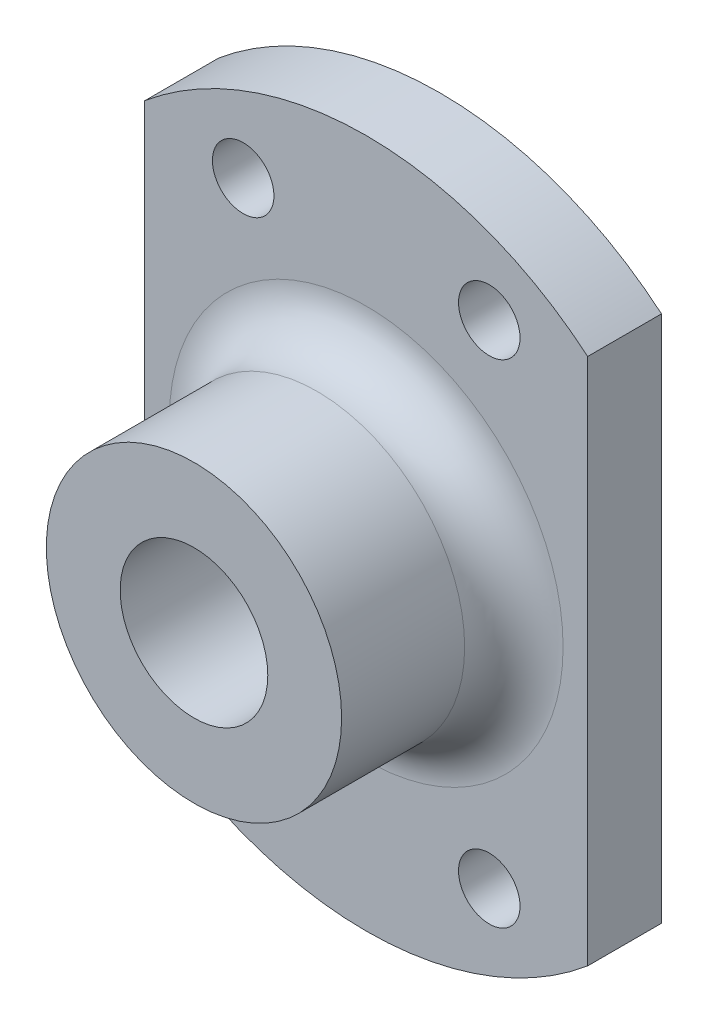
SolidWorks part; units mm, degrees
ref_plane "Front Plane" through (0, 0, 0) normal (0, 0, 1) x (1, 0, 0)
ref_plane "Top Plane" through (0, 0, 0) normal (0, 1, 0) x (1, 0, 0)
ref_plane "Right Plane" through (0, 0, 0) normal (1, 0, 0) x (0, 0, -1)
sketch "Sketch1" plane through (0, 0, 0) normal (0, 0, 1) x (1, 0, 0)
  line L0 (-9, 10.7238) -> (-9, -10.7238)
  line L1 (9, 10.7238) -> (9, -10.7238)
  line L2 (-9, 0) -> (9, 0) construction
  line L3 (-5, 10) -> (5, -10) construction
  line L4 (-5, -10) -> (5, 10) construction
  arc A0 (9, 10.7238) -> (-9, 10.7238) centre (0, 0) ccw
  arc A1 (-9, -10.7238) -> (9, -10.7238) centre (0, 0) ccw
  circle A2 centre (0, 0) radius 3
  circle A3 centre (-5, 10) radius 1.25
  circle A4 centre (5, 10) radius 1.25
  circle A5 centre (-5, -10) radius 1.25
  circle A6 centre (5, -10) radius 1.25
  point P7 (0, 0)
  point P18 (0, 0)
  dimension "D2" = 14
  dimension "D3" = 6
  dimension "D6" = 2.5
  dimension "D1" = 18
  dimension "D4" = 20
  dimension "D5" = 10
extrude "Main" add sketch "Sketch1" along normal blind 3
sketch "Sketch2" plane through (0, 0, 3) normal (0, 0, 1) x (1, 0, 0)
  circle A0 centre (0, 0) radius 6
  circle A1 centre (0, 0) radius 3
  circle A2 centre (0, 0) radius 3 construction
  dimension "D1" = 12
extrude "LinearBallSupport" add sketch "Sketch2" along normal blind 7
fillet "Fillet1" radius 2 1 edges at (6, 0, 3)
ref_plane "Plane1" through (14, 0, 0) normal (1, 0, 0) x (0, 0, -1)
